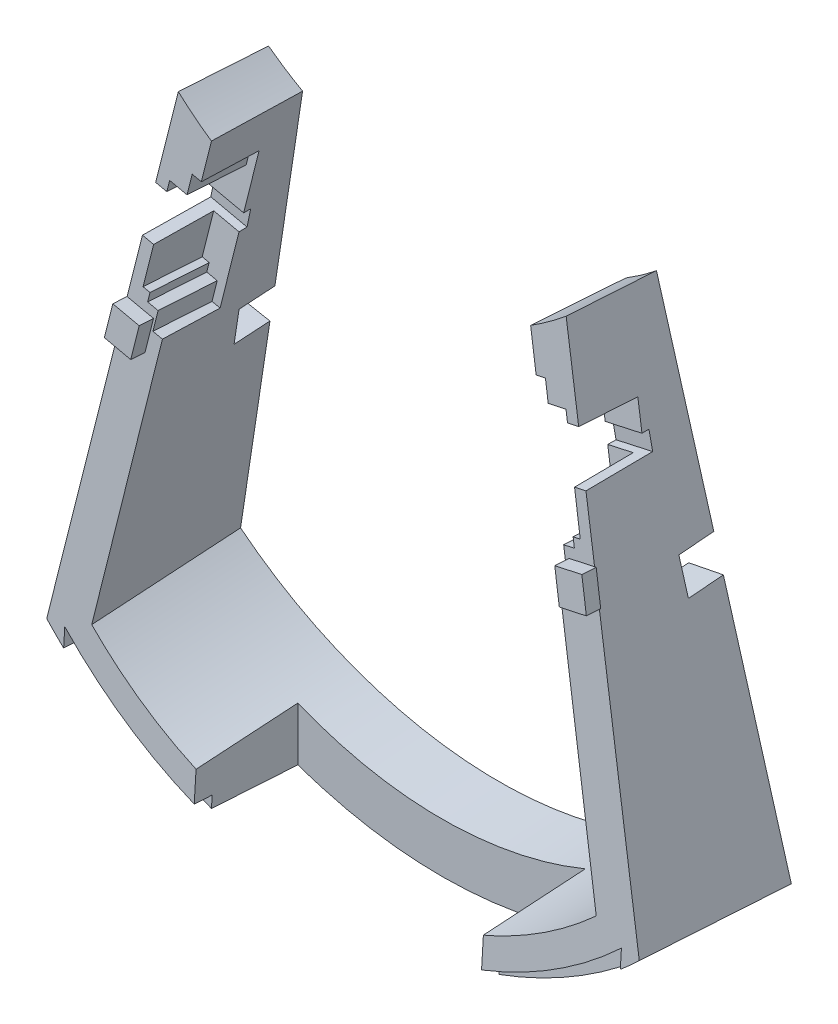
SolidWorks part; units mm, degrees
material "Oak"
ref_plane "Front Plane" through (0, 0, 0) normal (0, 0, 1) x (1, 0, 0)
ref_plane "Top Plane" through (0, 0, 0) normal (0, 1, 0) x (1, 0, 0)
ref_plane "Right Plane" through (0, 0, 0) normal (1, 0, 0) x (0, 0, -1)
sketch "Sketch2" plane through (0, 0, 0) normal (1, 0, 0) x (0, 0, -1)
  line L0 (-42.946, 177.4471) -> (-53.975, -0.0105)
  line L1 (-42.946, 177.4471) -> (-11.196, 177.4471)
  line L4 (-11.196, 177.4471) -> (0, 0)
  line L5 (-53.975, -0.0105) -> (-57.52, -57.0504)
  line L6 (-57.52, -57.0504) -> (3.3781, -53.5396)
  line L7 (3.3781, -53.5396) -> (0, 0)
  point P8 (-27.071, -55.295)
  point P9 (-27.071, 177.4471)
  dimension "D1" = 31.75
  dimension "D2" = 53.975
  dimension "D3" = 177.8
  dimension "D4" = 57.15
extrude "Boss-Extrude1" add sketch "Sketch2" along normal blind 209.55
sketch "Sketch1" plane through (0, 0, 0) normal (0, 0, 1) x (1, 0, 0)
  line L0 (0, 0) -> (34.925, 174.3361)
  line L1 (174.625, 174.3361) -> (209.55, 0)
  line L2 (0, 0) -> (209.55, 0) construction
  line L3 (104.775, 148.9361) -> (104.775, -41.5639) construction
  line L5 (-12.8433, 191.6723) -> (227.6672, 191.6723)
  line L6 (-12.8433, 191.6723) -> (-12.8433, -74.1551)
  line L7 (-12.8433, -74.1551) -> (227.6672, -74.1551)
  line L8 (227.6672, 191.6723) -> (227.6672, -74.1551)
  arc A2 (0, 0) -> (209.55, 0) centre (104.775, 111.2775) ccw
  arc A3 (34.925, 174.3361) -> (174.625, 174.3361) centre (104.775, 257.6799) ccw
  dimension "D1" = 139.7
  dimension "D2" = 177.8
  dimension "D3" = 209.55
  dimension "D4" = 190.5
  dimension "D5" = 25.4
ref_plane "Plane1" through (0, -2.5668, -41.2999) normal (0, 0.062, 0.9981) x (1, 0, 0)
sketch "Sketch3" plane through (0, 3.3416, 53.7667) normal (0, 0.062, 0.9981) x (1, 0, 0)
  line L0 (172.9017, 173.982) -> (209.55, 0)
  line L1 (0, 0) -> (35.7418, 174.1705)
  line L2 (104.775, 148.6493) -> (104.775, -41.4838) construction
  line L4 (-12.8433, 191.3032) -> (227.6672, 191.3032)
  line L5 (-12.8433, 191.3032) -> (-12.8433, -74.0123)
  line L6 (-12.8433, -74.0123) -> (227.6672, -74.0123)
  line L7 (227.6672, 191.3032) -> (227.6672, -74.0123)
  arc A0 (172.9017, 173.982) -> (35.7418, 174.1705) centre (104.4363, 257.4428) cw
  arc A1 (209.55, 0) -> (0, 0) centre (104.775, 110.6705) cw
  point P13 (104.775, -41.7295)
  dimension "D2" = 107.95
  dimension "D3" = 152.4
  dimension "D1" = 177.8
  dimension "D4" = 137.16
  dimension "D5" = 215.9
extrude "Cut-Extrude1" cut sketch "Sketch3" against normal through all
sketch "Sketch4" plane through (0, 0, 0) normal (0, 0.063, -0.998) x (-1, 0, 0)
  line L0 (-160.869, 170.8463) -> (-193.9794, 12.4218)
  line L1 (-15.5706, 12.4218) -> (-48.0037, 170.8463)
  line L2 (-209.55, 0) -> (-172.9017, 175.352) construction
  line L4 (-160.869, 170.8463) -> (-48.0037, 170.8463)
  arc A0 (-193.9794, 12.4218) -> (-15.5706, 12.4218) centre (-104.775, 111.5419) ccw
  ellipse E0 centre (-104.4363, 262.1521) end of major axis (-212.3863, 262.1521) minor radius 107.1066 (-172.9017, 179.3434) -> (-35.7418, 179.5304) ccw construction
  ellipse E1 centre (-104.775, 111.5419) end of major axis (-104.775, -42.0581) minor radius 152.4 (-209.55, 0) -> (0, 0) ccw construction
  dimension "D2" = 133.35
  dimension "D1" = 12.7
extrude "Cut-Extrude2" cut sketch "Sketch4" against normal through all
sketch "Sketch5" plane through (0, 0, 0) normal (0, 0.063, -0.998) x (-1, 0, 0)
  line L0 (-189.5756, 100.9986) -> (-176.0575, 98.1733)
  line L2 (-193.9794, 12.4218) -> (-161.6318, 167.1964) construction
  line L3 (-176.0575, 98.1733) -> (-178.6556, 85.7419)
  line L4 (-178.6556, 85.7419) -> (-192.1737, 88.5672)
  line L5 (-192.1737, 88.5672) -> (-189.5756, 100.9986)
  line L6 (-33.1258, 98.1733) -> (-19.4922, 100.9645)
  line L7 (-15.5706, 12.4218) -> (-47.2547, 167.1877) construction
  line L9 (-19.4922, 100.9645) -> (-16.9472, 88.5331)
  line L10 (-16.9472, 88.5331) -> (-30.5809, 85.7419)
  line L11 (-30.5809, 85.7419) -> (-33.1258, 98.1733)
  line L13 (-209.55, 6.7206) -> (-172.9017, 179.3434) construction
  line L14 (-35.7418, 179.5304) -> (0, 6.7206) construction
  dimension "D1" = 76.2
  dimension "D2" = 12.7
extrude "Cut-Extrude3" cut sketch "Sketch5" against normal blind 12.7
ref_plane "Plane2" through (0, 3.3416, 53.7667) normal (0, 0.062, 0.9981) x (1, 0, 0)
sketch "Sketch6" plane through (0, 3.3416, 53.7667) normal (0, 0.062, 0.9981) x (1, 0, 0)
  line L0 (6.35, -5.6836) -> (6.35, 0.6664)
  line L1 (203.2, 0.6664) -> (203.2, -5.6836)
  arc A0 (0, 0) -> (209.55, 0) centre (104.775, 110.6705) ccw construction
  arc A1 (6.35, 0.6664) -> (203.2, 0.6664) centre (104.775, 105.6466) ccw
  arc A2 (203.2, -5.6836) -> (6.35, -5.6836) centre (104.775, 110.6705) cw
  ellipse E0 centre (104.775, 105.6466) end of major axis (104.775, -28.7534) minor radius 133.35 (15.5706, 5.7461) -> (193.9794, 5.7461) ccw construction
  dimension "D1" = 6.35
  dimension "D2" = 6.35
  dimension "D3" = 6.35
extrude "Cut-Extrude4" cut sketch "Sketch6" against normal blind 6.35
sketch "Sketch7" plane through (0, 0, 0) normal (0, 1, 0) x (1, 0, 0)
  line L0 (53.975, -56.3552) -> (53.975, -18.8902)
  line L1 (53.975, -18.8902) -> (155.575, -18.8902)
  line L2 (155.575, -18.8902) -> (155.575, -56.3552)
  line L3 (155.575, -56.3552) -> (53.975, -56.3552)
  ellipse E1 centre (104.775, -46.9017) end of major axis (-47.625, -46.9017) minor radius 9.4534 (0, -53.7667) -> (6.35, -54.1192) ccw construction
  point P9 (104.775, -56.3552)
  dimension "D1" = 101.6
  dimension "D2" = 37.465
extrude "Cut-Extrude5" cut sketch "Sketch7" against normal through all and the other way through all
ref_plane "Plane3" through (21.1111, 21.0692, 1.3294) normal (0.7071, 0.7057, 0.0445) x (0, 0.063, -0.998)
ref_plane "Plane5" through (104.775, 0, 0) normal (-1, 0, 0) x (0, 0, 1)
sketch "Sketch10" plane through (200.6471, 42.1838, -2.6217) normal (0.9785, 0.2057, -0.0128) x (-0.0125, -0.0026, -0.9999)
  line L5 (-34.7745, 102.2358) -> (-32.6698, 136.8429) construction
  line L6 (-13.6647, 135.6871) -> (-45.5999, 137.6292) construction
  line L7 (-56.393, -39.8429) -> (-45.5999, 137.6292) construction
  circle A0 centre (-34.7745, 102.2358) radius 2.667
  dimension "D1" = 5.334
  dimension "D2" = 12.954
  dimension "D3" = 34.671
extrude "Cut-Extrude8" cut sketch "Sketch10" against normal blind 50.8
sketch "Sketch11" plane through (0, 0, 0) normal (-0.9796, 0.2006, -0.0125) x (-0.0122, 0.0025, 0.9999)
  line L5 (32.1584, 145.0974) -> (30.0361, 179.9578) construction
  line L6 (11.0547, 178.8022) -> (42.9661, 180.745) construction
  line L7 (42.9661, 180.745) -> (53.7708, 3.2736) construction
  circle A0 centre (32.1584, 145.0974) radius 2.667
  dimension "D1" = 5.334
  dimension "D2" = 12.954
  dimension "D3" = 34.925
extrude "Cut-Extrude9" cut sketch "Sketch11" against normal blind 50.8
ref_plane "Plane6" through (0, 2.3569, 37.9222) normal (0, 0.062, 0.9981) x (1, 0, 0)
sketch "Sketch12" plane through (0, 2.3569, 37.9222) normal (0, 0.062, 0.9981) x (1, 0, 0)
  line L0 (53.975, -33.0136) -> (53.975, -14.1148) construction
  line L1 (155.575, -18.6189) -> (155.575, -28.9925) construction
  circle A0 centre (53.975, -23.5642) radius 2.6933
  circle A1 centre (155.575, -23.8057) radius 2.6933
sketch "Sketch13" plane through (0, 3.3416, 53.7667) normal (0, 0.062, 0.9981) x (1, 0, 0)
  line L0 (21.844, 106.4462) -> (19.5463, 95.2495)
  line L1 (35.7418, 174.1705) -> (0, 0) construction
  line L2 (19.5463, 95.2495) -> (29.0013, 93.3093)
  line L3 (29.0013, 93.3093) -> (31.299, 104.5059)
  line L4 (31.299, 104.5059) -> (21.844, 106.4462)
  line L5 (104.775, -41.7295) -> (104.775, 110.6705) construction
  line L6 (178.251, 104.5059) -> (187.706, 106.4462)
  line L7 (180.5487, 93.3093) -> (178.251, 104.5059)
  line L8 (190.0037, 95.2495) -> (180.5487, 93.3093)
  line L9 (187.706, 106.4462) -> (190.0037, 95.2495)
  arc A0 (53.975, -33.0136) -> (155.575, -33.0136) centre (104.775, 110.6705) ccw construction
  dimension "D1" = 9.652
  dimension "D2" = 11.43
  dimension "D3" = 82.931
extrude "Boss-Extrude2" add sketch "Sketch13" along normal blind 5.08
sketch "Sketch14" plane through (0, 0, 0) normal (-0.9796, 0.2006, -0.0125) x (-0.0122, 0.0025, 0.9999)
  line L0 (45.523, 138.7474) -> (45.9096, 132.3974)
  line L1 (42.9661, 180.745) -> (47.1674, 111.7372) construction
  line L2 (45.9096, 132.3974) -> (22.028, 132.3974)
  line L3 (22.028, 132.3974) -> (22.028, 138.7474)
  line L4 (22.028, 138.7474) -> (45.523, 138.7474)
  circle A0 centre (32.1584, 145.0974) radius 2.667 construction
  dimension "D1" = 6.35
  dimension "D2" = 6.35
  dimension "D3" = 23.495
extrude "Cut-Extrude10" cut sketch "Sketch14" against normal blind 19.05 contours L4 L0 L2 L3
sketch "Sketch15" plane through (200.6471, 42.1838, -2.6217) normal (0.9785, 0.2057, -0.0128) x (-0.0125, -0.0026, -0.9999)
  line L0 (-48.1386, 95.8858) -> (-24.6436, 95.8858)
  line L1 (-49.7966, 68.6226) -> (-45.5999, 137.6292) construction
  line L2 (-24.6436, 95.8858) -> (-24.6436, 89.5358)
  line L3 (-24.6436, 89.5358) -> (-48.5248, 89.5358)
  line L4 (-48.5248, 89.5358) -> (-48.1386, 95.8858)
  circle A0 centre (-34.7745, 102.2358) radius 2.667 construction
  dimension "D1" = 6.35
  dimension "D2" = 23.495
  dimension "D3" = 6.35
extrude "Cut-Extrude11" cut sketch "Sketch15" against normal blind 19.05
sketch "Sketch16" plane through (0, 3.3416, 53.7667) normal (0, 0.062, 0.9981) x (1, 0, 0)
  line L0 (45.2734, 151.9765) -> (41.9766, 152.653)
  line L1 (40.8442, 130.1712) -> (48.0037, 165.418) construction
  line L2 (41.9766, 152.653) -> (40.5724, 145.8106)
  line L3 (40.5724, 145.8106) -> (34.3521, 147.0871)
  line L4 (34.3521, 147.0871) -> (33.5862, 143.3549)
  line L5 (33.5862, 143.3549) -> (29.5865, 144.1756)
  line L6 (35.7418, 174.1705) -> (27.2837, 132.954) construction
  line L7 (29.5865, 144.1756) -> (27.2837, 132.954)
  line L8 (27.2837, 132.954) -> (31.2834, 132.1332)
  line L9 (31.2834, 132.1332) -> (27.1399, 111.942)
  line L10 (27.1399, 111.942) -> (29.628, 111.4314)
  line L11 (29.628, 111.4314) -> (28.9884, 108.3145)
  line L12 (28.9884, 108.3145) -> (32.7206, 107.5486)
  line L13 (32.7206, 107.5486) -> (31.3165, 100.7062)
  line L14 (31.3165, 100.7062) -> (34.7188, 100.0151)
  line L15 (15.5706, 5.7461) -> (39.5779, 123.9368) construction
  line L16 (34.7188, 100.0151) -> (45.2734, 151.9765)
  line L17 (48.0037, 165.418) -> (45.2734, 151.9765) construction
  line L18 (40.8442, 130.1712) -> (27.2837, 132.954) construction
  line L19 (48.0037, 165.418) -> (160.869, 165.418) construction
  line L20 (104.4363, 165.418) -> (104.4363, 108.3145) construction
  line L21 (160.869, 165.418) -> (163.5992, 151.9765) construction
  line L22 (174.1538, 100.0151) -> (163.5992, 151.9765)
  line L23 (177.5561, 100.7062) -> (174.1538, 100.0151)
  line L24 (176.152, 107.5486) -> (177.5561, 100.7062)
  line L25 (179.8842, 108.3145) -> (176.152, 107.5486)
  line L26 (179.2446, 111.4314) -> (179.8842, 108.3145)
  line L27 (181.7327, 111.942) -> (179.2446, 111.4314)
  line L28 (177.5893, 132.1332) -> (181.7327, 111.942)
  line L29 (181.5889, 132.954) -> (177.5893, 132.1332)
  line L30 (179.2861, 144.1756) -> (181.5889, 132.954)
  line L31 (175.2865, 143.3549) -> (179.2861, 144.1756)
  line L32 (174.5206, 147.0871) -> (175.2865, 143.3549)
  line L33 (168.3002, 145.8106) -> (174.5206, 147.0871)
  line L34 (166.896, 152.653) -> (168.3002, 145.8106)
  line L35 (163.5992, 151.9765) -> (166.896, 152.653)
  point P33 (37.4623, 146.4488)
  dimension "D1" = 13.716
  dimension "D2" = 3.3655
  dimension "D3" = 6.35
  dimension "D4" = 6.985
  dimension "D5" = 3.81
  dimension "D6" = 53.0225
  dimension "D7" = 35.8775
  dimension "D8" = 3.81
extrude "Cut-Extrude12" cut sketch "Sketch16" against normal blind 20.955
sketch "Sketch9" plane through (21.1111, 21.0692, 1.3294) normal (0.7071, 0.7057, 0.0445) x (0, 0.063, -0.998)
  circle A0 centre (-61.45, -59.5731) radius 1.5875
  dimension "D1" = 3.175
sketch "Sketch17" plane through (0, 3.3668, 0.2124) normal (0, -0.063, 0.998) x (1, 0, 0)
  line L0 (45.2734, 154.1363) -> (48.0037, 167.4728) construction
  line L1 (46.7424, 161.3121) -> (162.1565, 161.3121)
  line L2 (46.7424, 161.3121) -> (46.7424, 162.5821)
  line L3 (46.7424, 162.5821) -> (162.1565, 162.5821)
  line L4 (162.1565, 161.3121) -> (162.1565, 162.5821)
  line L5 (160.869, 167.4728) -> (163.6539, 154.1474) construction
  dimension "D1" = 1.27
extrude "Boss-Extrude3" [suppressed] add sketch "Sketch17" along normal blind 20.955
sketch "Sketch18" plane through (0, 0, 0) normal (-0.9796, 0.2006, -0.0125) x (-0.0122, 0.0025, 0.9999)
  line L0 (34.3687, 149.545) -> (35.4127, 132.3974) construction
  line L1 (23.9106, 148.9083) -> (44.8269, 150.1817) construction
  line L2 (45.9096, 132.3974) -> (22.028, 132.3974) construction
  point P0 (34.8776, 141.1867)
sketch "Sketch19" plane through (200.6471, 42.1838, -2.6217) normal (0.9785, 0.2057, -0.0128) x (-0.0125, -0.0026, -0.9999)
  line L0 (-36.9921, 106.5677) -> (-36.5842, 89.5358) construction
  line L1 (-26.5339, 105.9316) -> (-47.4503, 107.2037) construction
  line L2 (-48.5248, 89.5358) -> (-24.6436, 89.5358) construction
ref_plane "Plane7" through (0, 2.6917, 43.3093) normal (0, -0.062, -0.9981) x (-0.201, -0.9777, 0.0608)
sketch "Sketch20" [suppressed] plane through (0, 2.6917, 43.3093) normal (0, -0.062, -0.9981) x (-0.201, -0.9777, 0.0608)
  line L0 (-138.8063, 0) -> (-138.8063, -13.3124) construction
  line L1 (-177.8, 0) -> (-102.0512, 0) construction
  line L2 (-157.9751, -13.274) -> (-137.0004, -13.3161) construction
  line L3 (-182.294, -69.2145) -> (19.8155, -111.0248) construction
  line L4 (-193.8416, -125.4861) -> (-170.7464, -12.9428) construction
  line L5 (-169.8372, -150.0021) -> (-164.5553, -137.7824) construction
  arc A0 (1.0656, -159.0357) -> (21.4895, -59.5097) centre (-129.4735, -80.3889) ccw construction
